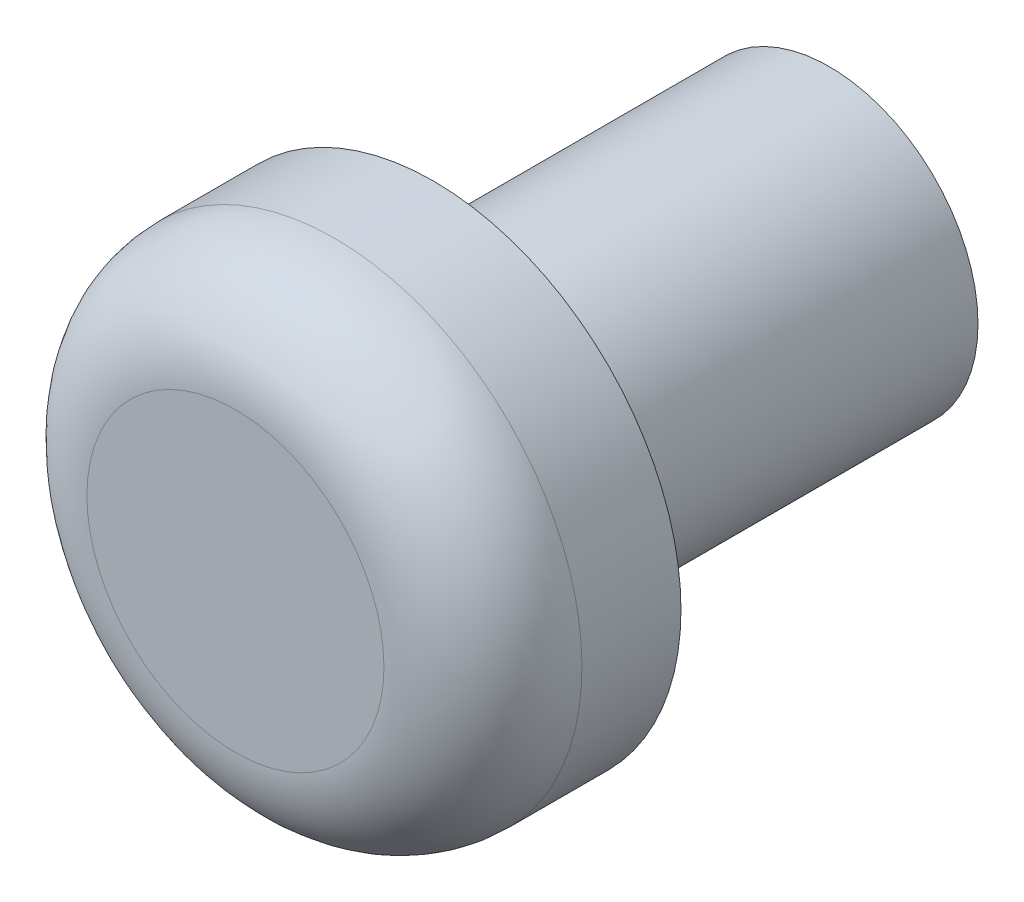
SolidWorks part; units mm, degrees
ref_plane "Front Plane" through (0, 0, 0) normal (0, 0, 1) x (1, 0, 0)
ref_plane "Top Plane" through (0, 0, 0) normal (0, 1, 0) x (1, 0, 0)
ref_plane "Right Plane" through (0, 0, 0) normal (1, 0, 0) x (0, 0, -1)
sketch "Sketch1" plane through (0, 0, 0) normal (0, 0, 1) x (1, 0, 0)
  circle A0 centre (0, 0) radius 2.5
  dimension "D1" = 5
extrude "Boss-Extrude1" add sketch "Sketch1" against normal blind 2
sketch "Sketch2" plane through (0, 0, -2) normal (0, 0, -1) x (-1, 0, 0)
  circle A0 centre (0, 0) radius 1.5
  dimension "D1" = 3
extrude "Boss-Extrude2" add sketch "Sketch2" along normal blind 4
fillet "Fillet2" radius 1 1 edges at (2.5, 0, 0)
sketch "Sketch3" plane through (0, 0, -6) normal (0, 0, -1) x (-1, 0, 0)
  circle A0 centre (0, 0) radius 0.5
  dimension "D1" = 1
extrude "Cut-Extrude1" cut sketch "Sketch3" against normal blind 2
